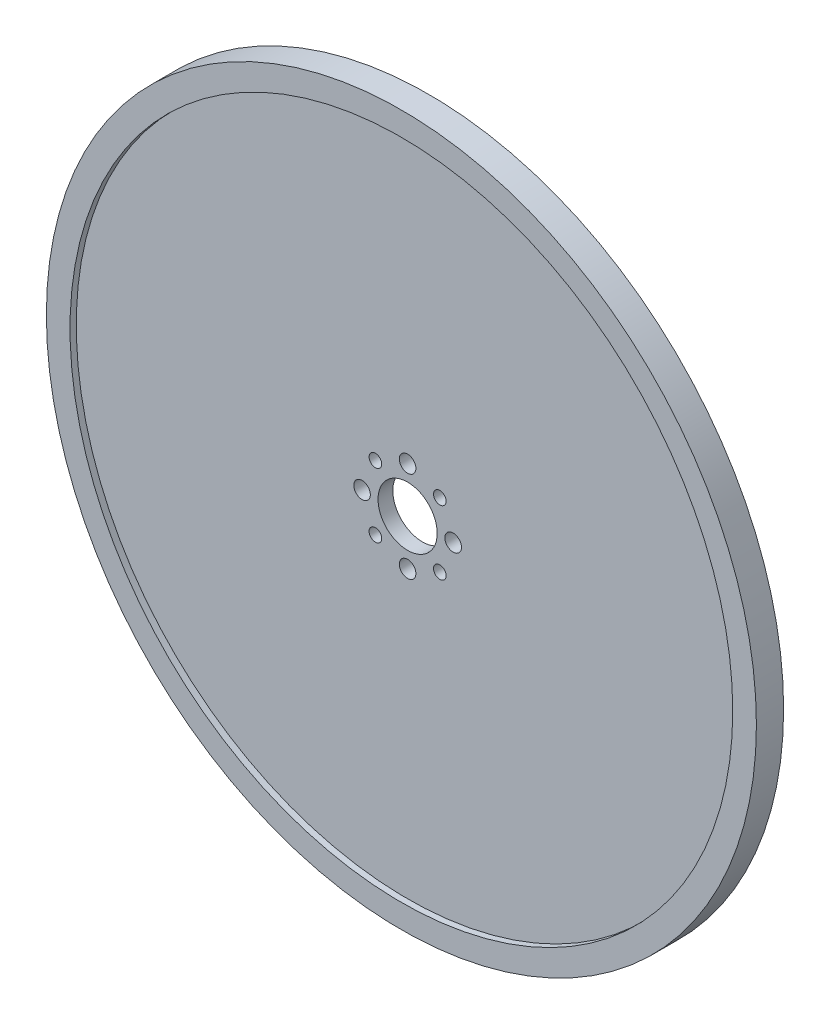
SolidWorks part; units mm, degrees
ref_plane "Front Plane" through (0, 0, 0) normal (0, 0, 1) x (1, 0, 0)
ref_plane "Top Plane" through (0, 0, 0) normal (0, 1, 0) x (1, 0, 0)
ref_plane "Right Plane" through (0, 0, 0) normal (1, 0, 0) x (0, 0, -1)
sketch "Sketch1" plane through (0, 0, 0) normal (0, 0, 1) x (1, 0, 0)
  circle A0 centre (0, 0) radius 76.2
  circle A1 centre (0, 0) radius 71.12
  dimension "D1" = 152.4
  dimension "D2" = 142.24
extrude "Boss-Extrude1" add sketch "Sketch1" along normal mid plane 5.842
sketch "Sketch3" plane through (0, 0, 0) normal (0, 0, 1) x (1, 0, 0)
  circle A0 centre (0, 0) radius 71.12
  circle A1 centre (0, 0) radius 6.35
  circle A2 centre (0, 9.779) radius 1.778
  circle A3 centre (9.779, 0) radius 1.778
  circle A4 centre (0, -9.779) radius 1.778
  circle A5 centre (-9.779, 0) radius 1.778
  dimension "D1" = 12.7
  dimension "D2" = 3.556
  dimension "D5" = 142.24
  dimension "D3" = 9.779
  dimension "D4" = 4
extrude "Boss-Extrude2" add sketch "Sketch3" along normal mid plane 3.175
hole_wizard "#6-32 Tapped Hole1" positions "Sketch5" profile "Sketch4" tap size "#6-32" standard "Ansi Inch" end condition up to next
sketch "Sketch5" plane through (0, 0, 1.5875) normal (0, 0, 1) x (1, 0, 0)
  line L0 (0, 0) -> (-6.9148, 6.9148) construction
  point P0 (-6.9148, 6.9148)
  point P12 (6.9148, 6.9148)
  point P13 (6.9148, -6.9148)
  point P14 (-6.9148, -6.9148)
  dimension "D1" = 4
sketch "Sketch4" plane through (-6.9148, 6.9148, 1.5875) normal (1, 0, 0) x (0, -1, 0)
  line L0 (0, 0) -> (0, 3.175)
  line L1 (0, 3.175) -> (1.3525, 3.175)
  line L2 (1.3525, 3.175) -> (1.3525, 0)
  line L5 (1.3525, 0) -> (0, 0)
  line L11 (0, -6.35) -> (0, 107.95) construction
  dimension "Thread Major Dia." = 2.7051
  dimension "Thru Tap Drill Depth" = 3.175
